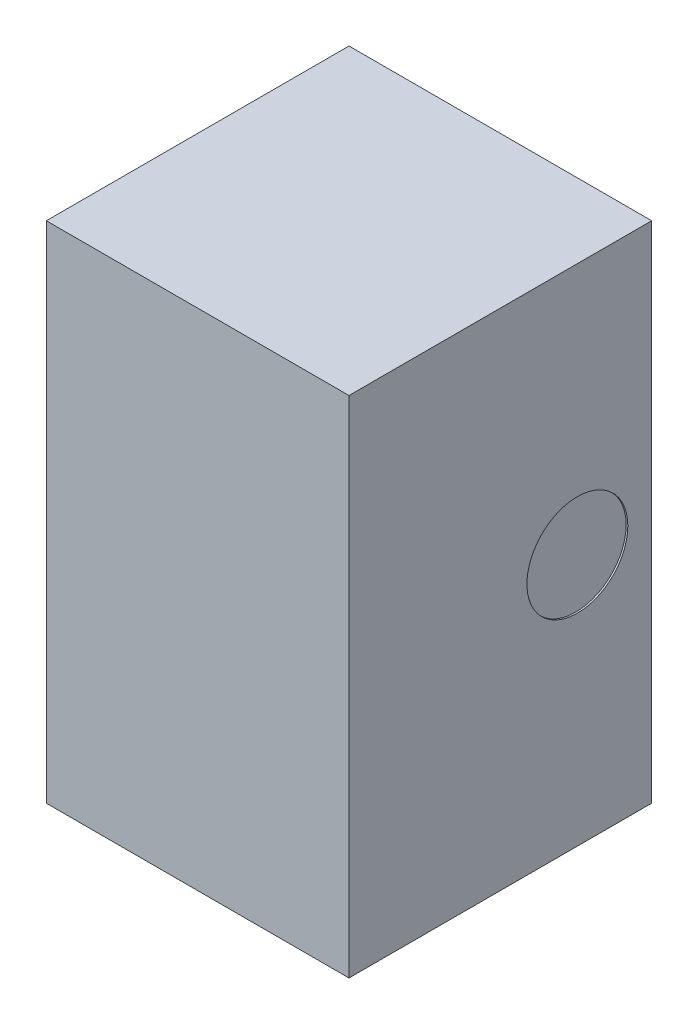
SolidWorks part; units mm, degrees
ref_plane "Front Plane" through (0, 0, 0) normal (0, 0, 1) x (1, 0, 0)
ref_plane "Top Plane" through (0, 0, 0) normal (0, 1, 0) x (1, 0, 0)
ref_plane "Right Plane" through (0, 0, 0) normal (1, 0, 0) x (0, 0, -1)
sketch "Sketch1" plane through (0, 0, 0) normal (0, 1, 0) x (1, 0, 0)
  line L0 (0, 0) -> (18.6879, 0) construction
  line L1 (0, 0) -> (0, -14.4281) construction
  line L3 (-0.45, 0.45) -> (0.45, 0.45)
  line L4 (-0.45, 0.45) -> (-0.45, -0.45)
  line L5 (-0.45, -0.45) -> (0.45, -0.45)
  line L6 (0.45, 0.45) -> (0.45, -0.45)
  dimension "D1" = 0.9
extrude "Boss-Extrude1" add sketch "Sketch1" along normal blind 1.5
ref_plane "Plane1" through (0.45, 0, 0) normal (1, 0, 0) x (0, 0, -1)
sketch "Sketch2" plane through (0.45, 0, 0) normal (1, 0, 0) x (0, 0, -1)
  line L0 (-0.45, 0.75) -> (0.45, 0.75) construction
  line L1 (-0.45, 1.5) -> (-0.45, 0) construction
  line L2 (0.45, 1.5) -> (0.45, 0) construction
  circle A0 centre (0.229, 0.75) radius 0.15
extrude "Cut-Extrude1" cut sketch "Sketch2" against normal blind 0.005 contours A0
